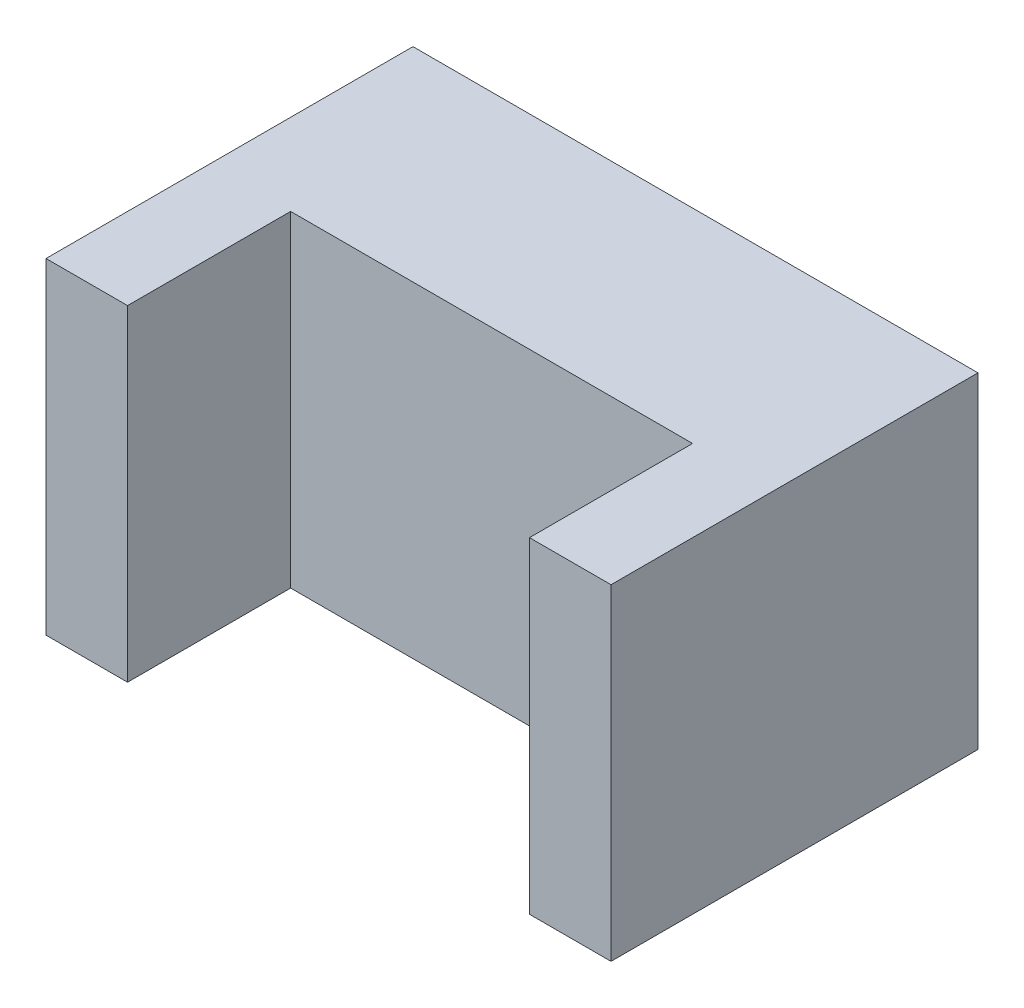
SolidWorks part; units mm, degrees
ref_plane "Front Plane" through (0, 0, 0) normal (0, 0, 1) x (1, 0, 0)
ref_plane "Top Plane" through (0, 0, 0) normal (0, 1, 0) x (1, 0, 0)
ref_plane "Right Plane" through (0, 0, 0) normal (1, 0, 0) x (0, 0, -1)
sketch "Sketch2" plane through (0, 0, 0) normal (0, 1, 0) x (1, 0, 0)
  line L0 (-2.6429, 0) -> (-2.6429, 4.5)
  line L1 (-2.6429, 4.5) -> (4.2857, 4.5)
  line L2 (4.2857, 4.5) -> (4.2857, 0)
  line L3 (4.2857, 0) -> (3.2857, 0)
  line L4 (3.2857, 0) -> (3.2857, 2)
  line L5 (3.2857, 2) -> (-1.6429, 2)
  line L6 (-1.6429, 2) -> (-1.6429, 0)
  line L7 (-1.6429, 0) -> (-2.6429, 0)
  dimension "D1" = 1
  dimension "D2" = 2.5
  dimension "D3" = 2
extrude "Boss-Extrude1" add sketch "Sketch2" along normal blind 4
